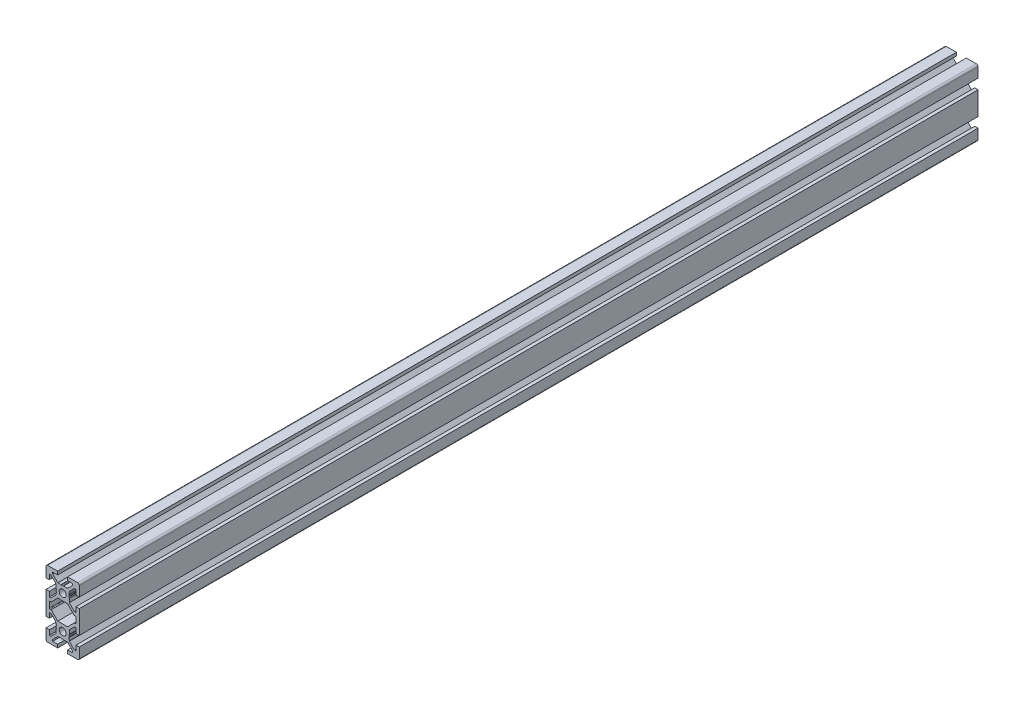
SolidWorks part; units mm, degrees
material "1060 Alloy"
ref_plane "Front Plane" through (0, 0, 0) normal (0, 0, 1) x (1, 0, 0)
ref_plane "Top Plane" through (0, 0, 0) normal (0, 1, 0) x (1, 0, 0)
ref_plane "Right Plane" through (0, 0, 0) normal (1, 0, 0) x (0, 0, -1)
ref_plane "Plane1" through (0, 0, -600) normal (0, 0, -1) x (-1, 0, 0)
sketch "Sketch1" plane through (0, 0, -600) normal (0, 0, -1) x (-1, 0, 0)
  line L0 (8, 1.7) -> (8, -1.7)
  line L1 (7.7, -2) -> (7.0636, -2)
  line L2 (6.8515, -2.0879) -> (2.9393, -6)
  line L3 (2.9393, -6) -> (-2.9393, -6)
  line L4 (-2.9393, -6) -> (-6.8515, -2.0879)
  line L5 (-7.0636, -2) -> (-7.7, -2)
  line L6 (-8, -1.7) -> (-8, 1.7)
  line L7 (-7.7, 2) -> (-7.0636, 2)
  line L8 (-6.8515, 2.0879) -> (-2.9393, 6)
  line L9 (-2.9393, 6) -> (2.9393, 6)
  line L10 (2.9393, 6) -> (6.8515, 2.0879)
  line L11 (7.0636, 2) -> (7.7, 2)
  line L12 (10, -7) -> (10, 7)
  line L13 (10, 7) -> (8, 7)
  line L14 (8, 7) -> (8, 4)
  line L15 (8, 4) -> (7.0607, 4)
  line L16 (7.0607, 4) -> (4, 7.0607)
  line L17 (4, 7.0607) -> (4, 7.5)
  line L18 (4, 7.5) -> (3.751, 8.7811)
  line L19 (3.751, 8.7811) -> (3.933, 9.0964)
  line L20 (3.933, 9.5964) -> (3.7, 10)
  line L21 (3.7, 10) -> (3.933, 10.4036)
  line L22 (4, 10.6536) -> (4, 12.9393)
  line L23 (4, 12.9393) -> (7.0607, 16)
  line L24 (7.0607, 16) -> (8, 16)
  line L25 (8, 16) -> (8, 13)
  line L26 (8, 13) -> (10, 13)
  line L27 (10, 13) -> (10, 19)
  line L28 (9, 20) -> (3, 20)
  line L29 (3, 20) -> (3, 18)
  line L30 (3, 18) -> (6, 18)
  line L31 (6, 18) -> (6, 17.0607)
  line L32 (6, 17.0607) -> (2.9393, 14)
  line L33 (2.9393, 14) -> (2.5, 14)
  line L34 (2.5, 14) -> (1.2189, 13.751)
  line L35 (1.2189, 13.751) -> (0.9036, 13.933)
  line L36 (0.4036, 13.933) -> (0, 13.7)
  line L37 (0, 13.7) -> (-0.4036, 13.933)
  line L38 (-0.6536, 14) -> (-2.9393, 14)
  line L39 (-2.9393, 14) -> (-6, 17.0607)
  line L40 (-6, 17.0607) -> (-6, 18)
  line L41 (-6, 18) -> (-3, 18)
  line L42 (-3, 18) -> (-3, 20)
  line L43 (-3, 20) -> (-9, 20)
  line L44 (-10, 19) -> (-10, 13)
  line L45 (-10, 13) -> (-8, 13)
  line L46 (-8, 13) -> (-8, 16)
  line L47 (-8, 16) -> (-7.0607, 16)
  line L48 (-7.0607, 16) -> (-4, 12.9393)
  line L49 (-4, 12.9393) -> (-4, 12.5)
  line L50 (-4, 12.5) -> (-3.751, 11.2189)
  line L51 (-3.751, 11.2189) -> (-3.933, 10.9036)
  line L52 (-3.933, 10.4036) -> (-3.7, 10)
  line L53 (-3.7, 10) -> (-3.933, 9.5964)
  line L54 (-4, 9.3464) -> (-4, 7.0607)
  line L55 (-4, 7.0607) -> (-7.0607, 4)
  line L56 (-7.0607, 4) -> (-8, 4)
  line L57 (-8, 4) -> (-8, 7)
  line L58 (-8, 7) -> (-10, 7)
  line L59 (-10, 7) -> (-10, -7)
  line L60 (-10, -7) -> (-8, -7)
  line L61 (-8, -7) -> (-8, -4)
  line L62 (-8, -4) -> (-7.0607, -4)
  line L63 (-7.0607, -4) -> (-4, -7.0607)
  line L64 (-4, -7.0607) -> (-4, -9.3464)
  line L65 (-3.933, -9.5964) -> (-3.7, -10)
  line L66 (-3.7, -10) -> (-3.933, -10.4036)
  line L67 (-3.933, -10.9036) -> (-3.751, -11.2189)
  line L68 (-3.751, -11.2189) -> (-4, -12.5)
  line L69 (-4, -12.5) -> (-4, -12.9393)
  line L70 (-4, -12.9393) -> (-7.0607, -16)
  line L71 (-7.0607, -16) -> (-8, -16)
  line L72 (-8, -16) -> (-8, -13)
  line L73 (-8, -13) -> (-10, -13)
  line L74 (-10, -13) -> (-10, -19)
  line L75 (-9, -20) -> (-3, -20)
  line L76 (-3, -20) -> (-3, -18)
  line L77 (-3, -18) -> (-6, -18)
  line L78 (-6, -18) -> (-6, -17.0607)
  line L79 (-6, -17.0607) -> (-2.9393, -14)
  line L80 (-2.9393, -14) -> (-0.6536, -14)
  line L81 (-0.4036, -13.933) -> (0, -13.7)
  line L82 (0, -13.7) -> (0.4036, -13.933)
  line L83 (0.9036, -13.933) -> (1.2189, -13.751)
  line L84 (1.2189, -13.751) -> (2.5, -14)
  line L85 (2.5, -14) -> (2.9393, -14)
  line L86 (2.9393, -14) -> (6, -17.0607)
  line L87 (6, -17.0607) -> (6, -18)
  line L88 (6, -18) -> (3, -18)
  line L89 (3, -18) -> (3, -20)
  line L90 (3, -20) -> (9, -20)
  line L91 (10, -19) -> (10, -13)
  line L92 (10, -13) -> (8, -13)
  line L93 (8, -13) -> (8, -16)
  line L94 (8, -16) -> (7.0607, -16)
  line L95 (7.0607, -16) -> (4, -12.9393)
  line L96 (4, -12.9393) -> (4, -10.6536)
  line L97 (3.933, -10.4036) -> (3.7, -10)
  line L98 (3.7, -10) -> (3.933, -9.5964)
  line L99 (3.933, -9.0964) -> (3.751, -8.7811)
  line L100 (3.751, -8.7811) -> (4, -7.5)
  line L101 (4, -7.5) -> (4, -7.0607)
  line L102 (4, -7.0607) -> (7.0607, -4)
  line L103 (7.0607, -4) -> (8, -4)
  line L104 (8, -4) -> (8, -7)
  line L105 (8, -7) -> (10, -7)
  circle A0 centre (0, -10) radius 2.1
  circle A1 centre (0, 10) radius 2.1
  arc A2 (7.7, 2) -> (8, 1.7) centre (7.7, 1.7) cw
  arc A3 (8, -1.7) -> (7.7, -2) centre (7.7, -1.7) cw
  arc A4 (7.0636, -2) -> (6.8515, -2.0879) centre (7.0636, -2.3) ccw
  arc A5 (-6.8515, -2.0879) -> (-7.0636, -2) centre (-7.0636, -2.3) ccw
  arc A6 (-7.7, -2) -> (-8, -1.7) centre (-7.7, -1.7) cw
  arc A7 (-8, 1.7) -> (-7.7, 2) centre (-7.7, 1.7) cw
  arc A8 (-7.0636, 2) -> (-6.8515, 2.0879) centre (-7.0636, 2.3) ccw
  arc A9 (6.8515, 2.0879) -> (7.0636, 2) centre (7.0636, 2.3) ccw
  arc A10 (3.933, 9.0964) -> (3.933, 9.5964) centre (3.5, 9.3464) ccw
  arc A11 (3.933, 10.4036) -> (4, 10.6536) centre (3.5, 10.6536) ccw
  arc A12 (10, 19) -> (9, 20) centre (9, 19) ccw
  arc A13 (0.9036, 13.933) -> (0.4036, 13.933) centre (0.6536, 13.5) ccw
  arc A14 (-0.4036, 13.933) -> (-0.6536, 14) centre (-0.6536, 13.5) ccw
  arc A15 (-9, 20) -> (-10, 19) centre (-9, 19) ccw
  arc A16 (-3.933, 10.9036) -> (-3.933, 10.4036) centre (-3.5, 10.6536) ccw
  arc A17 (-3.933, 9.5964) -> (-4, 9.3464) centre (-3.5, 9.3464) ccw
  arc A18 (-4, -9.3464) -> (-3.933, -9.5964) centre (-3.5, -9.3464) ccw
  arc A19 (-3.933, -10.4036) -> (-3.933, -10.9036) centre (-3.5, -10.6536) ccw
  arc A20 (-10, -19) -> (-9, -20) centre (-9, -19) ccw
  arc A21 (-0.6536, -14) -> (-0.4036, -13.933) centre (-0.6536, -13.5) ccw
  arc A22 (0.4036, -13.933) -> (0.9036, -13.933) centre (0.6536, -13.5) ccw
  arc A23 (9, -20) -> (10, -19) centre (9, -19) ccw
  arc A24 (4, -10.6536) -> (3.933, -10.4036) centre (3.5, -10.6536) ccw
  arc A25 (3.933, -9.5964) -> (3.933, -9.0964) centre (3.5, -9.3464) ccw
  dimension "D1" = 4.2
  dimension "D3" = 0.3
  dimension "D4" = 0.3
  dimension "D5" = 0.3
  dimension "D6" = 0.3
  dimension "D7" = 0.3
  dimension "D8" = 0.3
  dimension "D9" = 0.3
  dimension "D10" = 0.5
  dimension "D11" = 0.5
  dimension "D12" = 1
  dimension "D13" = 0.5
  dimension "D14" = 0.5
  dimension "D15" = 1
  dimension "D16" = 0.5
  dimension "D17" = 0.5
  dimension "D18" = 0.5
  dimension "D19" = 0.5
  dimension "D20" = 0.4036
  dimension "D21" = 0.5
  dimension "D22" = 0.5
  dimension "D23" = 1
  dimension "D24" = 0.5
  dimension "D25" = 0.5
  dimension "D26" = 0.4036
  dimension "D27" = 0.6536
  dimension "D28" = 0.6536
  dimension "D29" = 0.9036
  dimension "D30" = 0.9036
  dimension "D31" = 1.2189
  dimension "D32" = 1.2189
  dimension "D33" = 2.5
  dimension "D34" = 2.5
  dimension "D35" = 2.9393
  dimension "D36" = 2.9393
  dimension "D37" = 3
  dimension "D38" = 3.5
  dimension "D39" = 6
  dimension "D40" = 6.8515
  dimension "D41" = 3.7
  dimension "D42" = 3.7
  dimension "D43" = 3.751
  dimension "D44" = 3.751
  dimension "D45" = 3.933
  dimension "D46" = 3.933
  dimension "D47" = 6.8515
  dimension "D48" = 7.0607
  dimension "D49" = 7.0607
  dimension "D50" = 7.0636
  dimension "D51" = 7.0636
  dimension "D52" = 8
  dimension "D53" = 10
  dimension "D54" = 3
  dimension "D55" = 4
  dimension "D56" = 6
  dimension "D57" = 6.8515
  dimension "D58" = 6.8515
  dimension "D59" = 7.0607
  dimension "D60" = 7.0607
  dimension "D61" = 0.4036
  dimension "D62" = 0.4036
  dimension "D63" = 0.6536
  dimension "D64" = 0.6536
  dimension "D65" = 2.9393
  dimension "D66" = 2.9393
  dimension "D67" = 8
  dimension "D68" = 2
  dimension "D69" = 3.5
  dimension "D70" = 3.5
  dimension "D71" = 3.7
  dimension "D72" = 3.7
  dimension "D73" = 3.751
  dimension "D74" = 3.751
  dimension "D75" = 3.933
  dimension "D76" = 3.933
  dimension "D77" = 4
  dimension "D78" = 6
  dimension "D79" = 7
  dimension "D80" = 7.0607
  dimension "D81" = 7.0607
  dimension "D82" = 7.5
  dimension "D83" = 8.7811
  dimension "D84" = 9.0964
  dimension "D85" = 9.3464
  dimension "D86" = 9.3464
  dimension "D87" = 9.5964
  dimension "D88" = 9.5964
  dimension "D89" = 10.4036
  dimension "D90" = 12.5
  dimension "D91" = 13
  dimension "D92" = 13.5
  dimension "D93" = 13.5
  dimension "D94" = 18
  dimension "D95" = 20
  dimension "D96" = 2
  dimension "D97" = 4
  dimension "D98" = 6
  dimension "D99" = 7
  dimension "D100" = 7.0607
  dimension "D101" = 7.0607
  dimension "D102" = 7.5
  dimension "D103" = 8.7811
  dimension "D104" = 9.0964
  dimension "D105" = 9.3464
  dimension "D106" = 9.3464
  dimension "D107" = 9.5964
  dimension "D108" = 9.5964
  dimension "D109" = 10.4036
  dimension "D110" = 12.5
  dimension "D111" = 13
  dimension "D112" = 18
extrude "Boss-Extrude1" add sketch "Sketch1" against normal blind 540
sketch "Sketch2" plane through (10, 0, 0) normal (1, 0, 0) x (0, 0, -1)
  line L0 (60, 13) -> (60, 7) construction
  line L1 (60, 10) -> (70, 10) construction
  line L2 (60, -7) -> (60, -13) construction
  line L3 (60, -10) -> (70, -10) construction
  circle A0 centre (70, 10) radius 2
  circle A1 centre (70, -10) radius 2
  dimension "D3" = 4
  dimension "D4" = 4
  dimension "D1" = 10
  dimension "D2" = 10
extrude "Cut-Extrude1" cut sketch "Sketch2" against normal through all
ref_plane "Plane2" through (0, 0, -330) normal (0, 0, 1) x (1, 0, 0)
mirror "Mirror1" about plane through (0, 0, -330) normal (0, 0, 1) of "Cut-Extrude1"
